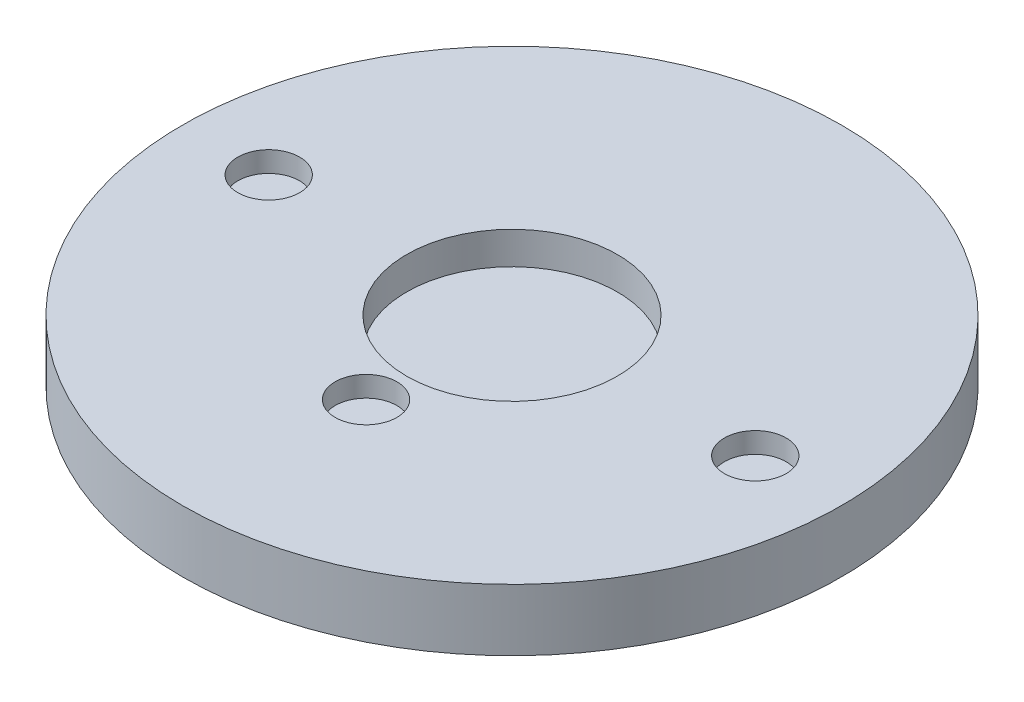
SolidWorks part; units mm, degrees
ref_plane "Front Plane" through (0, 0, 0) normal (0, 0, 1) x (1, 0, 0)
ref_plane "Top Plane" through (0, 0, 0) normal (0, 1, 0) x (1, 0, 0)
ref_plane "Right Plane" through (0, 0, 0) normal (1, 0, 0) x (0, 0, -1)
sketch "Sketch1" plane through (0, 0, 0) normal (0, 1, 0) x (1, 0, 0)
  circle A0 centre (0, 0) radius 101.6
  dimension "D1" = 203.2
extrude "Boss-Extrude1" add sketch "Sketch1" along normal blind 19.05
sketch "Sketch2" plane through (0, 19.05, 0) normal (0, 1, 0) x (1, 0, 0)
  circle A0 centre (0, 0) radius 32.5
  dimension "D1" = 65
extrude "Cut-Extrude1" cut sketch "Sketch2" against normal blind 10
sketch "Sketch4" plane through (0, 19.05, 0) normal (0, 1, 0) x (1, 0, 0)
  circle A0 centre (-75, 0) radius 9.525
  circle A1 centre (0, 0) radius 101.6 construction
  dimension "D1" = 19.05
  dimension "D2" = 75
extrude "Cut-Extrude3" cut sketch "Sketch4" against normal blind 6.35
sketch "Sketch5" plane through (0, 19.05, 0) normal (0, 1, 0) x (1, 0, 0)
  circle A0 centre (75, 0) radius 9.525
  circle A1 centre (0, 0) radius 101.6 construction
  dimension "D1" = 19.05
  dimension "D2" = 75
extrude "Cut-Extrude4" cut sketch "Sketch5" against normal blind 6.35
sketch "Sketch6" plane through (0, 19.05, 0) normal (0, 1, 0) x (1, 0, 0)
  circle A0 centre (0, -45) radius 9.525
  dimension "D1" = 19.05
  dimension "D2" = 45
extrude "Cut-Extrude5" cut sketch "Sketch6" against normal blind 6.35
